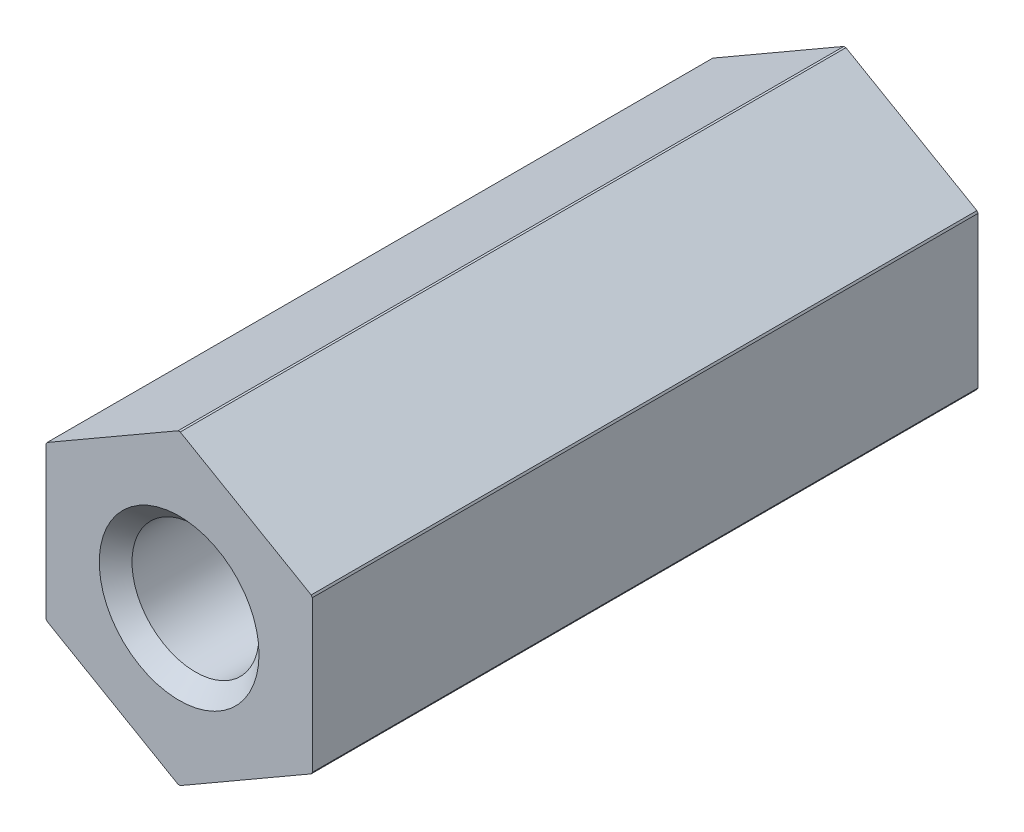
SolidWorks part; units mm, degrees
ref_plane "Front Plane" through (0, 0, 0) normal (0, 0, 1) x (1, 0, 0)
ref_plane "Top Plane" through (0, 0, 0) normal (0, 1, 0) x (1, 0, 0)
ref_plane "Right Plane" through (0, 0, 0) normal (1, 0, 0) x (0, 0, -1)
ref_plane "Plane1" through (0, 0, 0) normal (1, 0, 0) x (0, 0, -1)
sketch "Sketch1" plane through (0, 0, 0) normal (1, 0, 0) x (0, 0, -1)
  line L0 (-25, 3) -> (-24.3857, 2.3857)
  line L1 (-24.3857, 2.3857) -> (-1.3174, 2.3857)
  line L2 (-1.3174, 2.3857) -> (0, 3)
  line L3 (0, 3) -> (0, 5.75)
  line L4 (0, 5.75) -> (-25, 5.75)
  line L5 (-25, 5.75) -> (-25, 3)
  line L6 (0, 0) -> (-25, 0) construction
  line L7 (0, 0) -> (0, 3) construction
  dimension "D1" = 11.5
  dimension "D2" = 25
  dimension "D3" = 6
  dimension "D4" = 4.7713
revolve "Revolve1" add sketch "Sketch1" angle 360 about L6
ref_plane "Plane2" through (0, 0, 0) normal (0, 0, 1) x (1, 0, 0)
sketch "Sketch2" plane through (0, 0, 0) normal (0, 0, 1) x (1, 0, 0)
  line L0 (-10, -10) -> (10, -10)
  line L1 (10, -10) -> (10, 10)
  line L2 (10, 10) -> (-10, 10)
  line L3 (-10, 10) -> (-10, -10)
  line L4 (-5, 2.8868) -> (-5, -2.8868)
  line L5 (-5, -2.8868) -> (0, -5.7735)
  line L6 (0, -5.7735) -> (5, -2.8868)
  line L7 (5, -2.8868) -> (5, 2.8868)
  line L8 (5, 2.8868) -> (0, 5.7735)
  line L9 (0, 5.7735) -> (-5, 2.8868)
extrude "Cut-Extrude1" cut sketch "Sketch2" along normal blind 25
